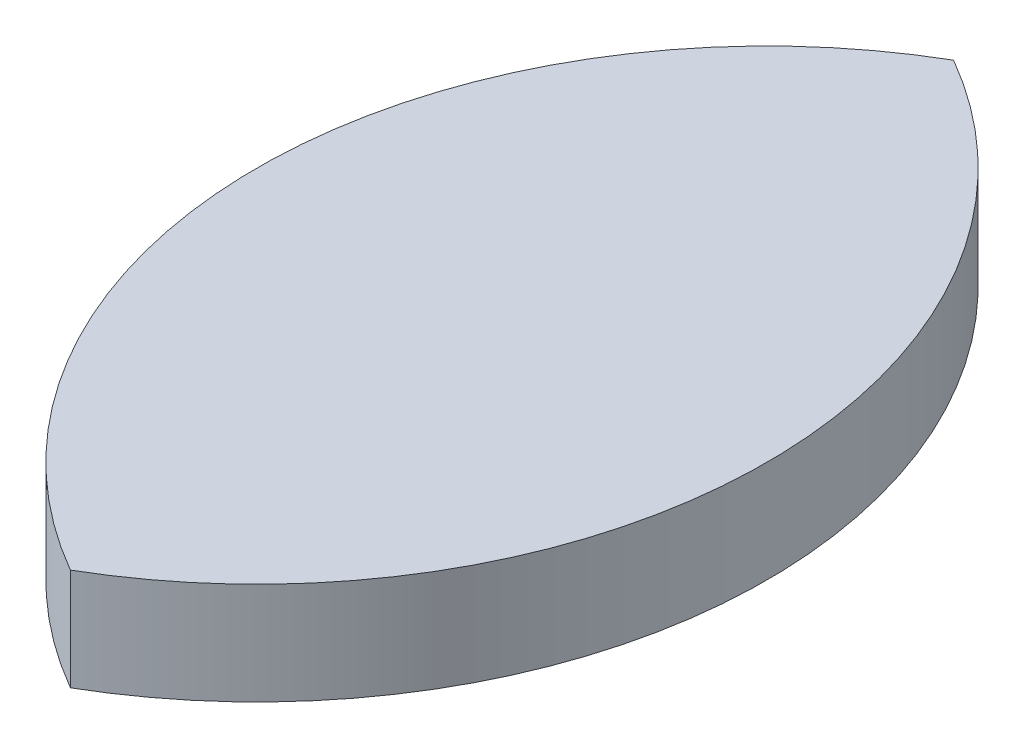
SolidWorks part; units mm, degrees
ref_plane "Front Plane" through (0, 0, 0) normal (0, 0, 1) x (1, 0, 0)
ref_plane "Top Plane" through (0, 0, 0) normal (0, 1, 0) x (1, 0, 0)
ref_plane "Right Plane" through (0, 0, 0) normal (1, 0, 0) x (0, 0, -1)
sketch "Sketch1" plane through (0, 0, 0) normal (0, 1, 0) x (1, 0, 0)
  arc A0 (25, -43.3013) -> (25, 43.3013) centre (0, 0) ccw
  arc A1 (25, 43.3013) -> (25, -43.3013) centre (50, 0) ccw
extrude "Boss-Extrude2" add sketch "Sketch1" along normal blind 10
